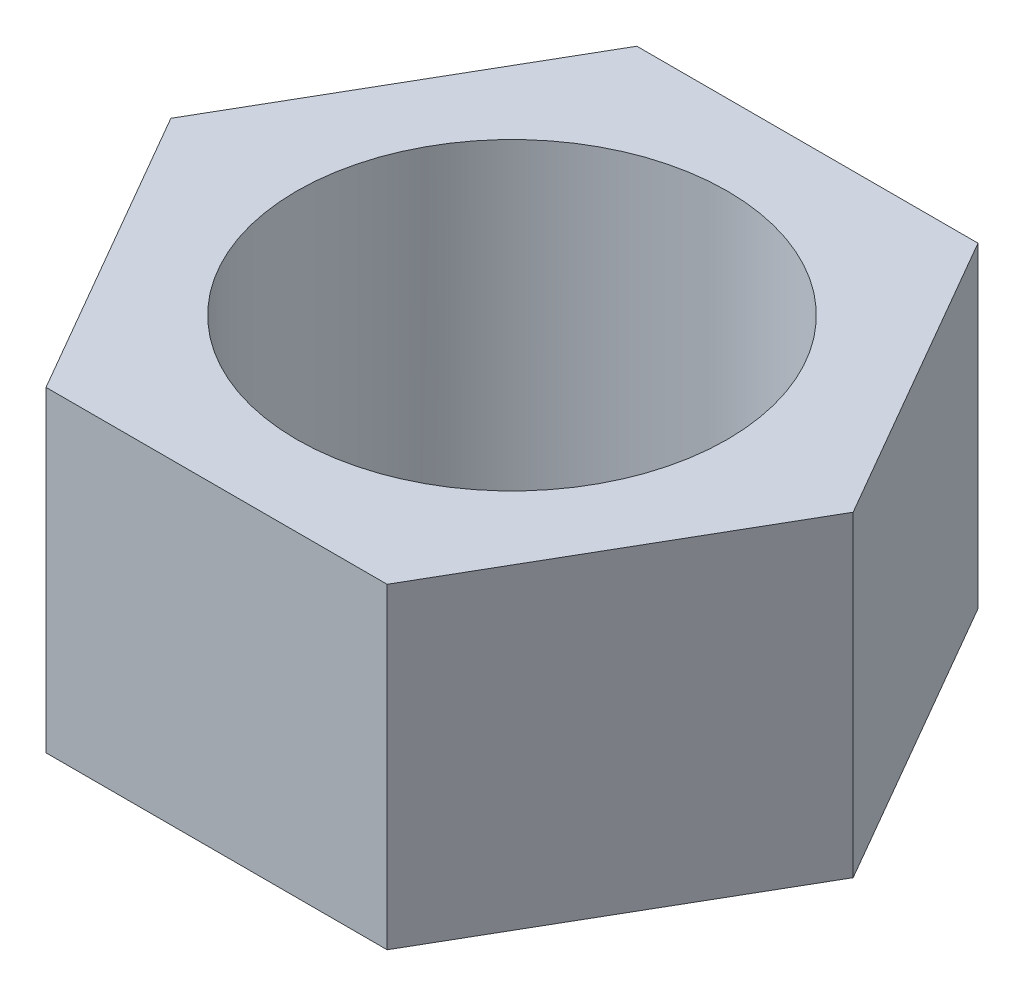
SolidWorks part; units mm, degrees
material "Plain Carbon Steel"
ref_plane "Front Plane" through (0, 0, 0) normal (0, 0, 1) x (1, 0, 0)
ref_plane "Top Plane" through (0, 0, 0) normal (0, 1, 0) x (1, 0, 0)
ref_plane "Right Plane" through (0, 0, 0) normal (1, 0, 0) x (0, 0, -1)
sketch "Sketch1" plane through (0, 0, 0) normal (0, 1, 0) x (1, 0, 0)
  line L1 (4.0415, 0) -> (2.0207, 3.5)
  line L2 (2.0207, 3.5) -> (-2.0207, 3.5)
  line L3 (-2.0207, 3.5) -> (-4.0415, 0)
  line L4 (-4.0415, 0) -> (-2.0207, -3.5)
  line L5 (-2.0207, -3.5) -> (2.0207, -3.5)
  line L6 (2.0207, -3.5) -> (4.0415, 0)
  circle A0 centre (0, 0) radius 3.5 construction
  dimension "D1" = 7
extrude "Boss-Extrude1" add sketch "Sketch1" along normal blind 3.75
sketch "Sketch3" plane through (0, 0, 0) normal (0, -1, 0) x (1, 0, 0)
  circle A0 centre (0, 0) radius 2.55
  dimension "D1" = 5.1
extrude "Cut-Extrude1" cut sketch "Sketch3" against normal blind 10
